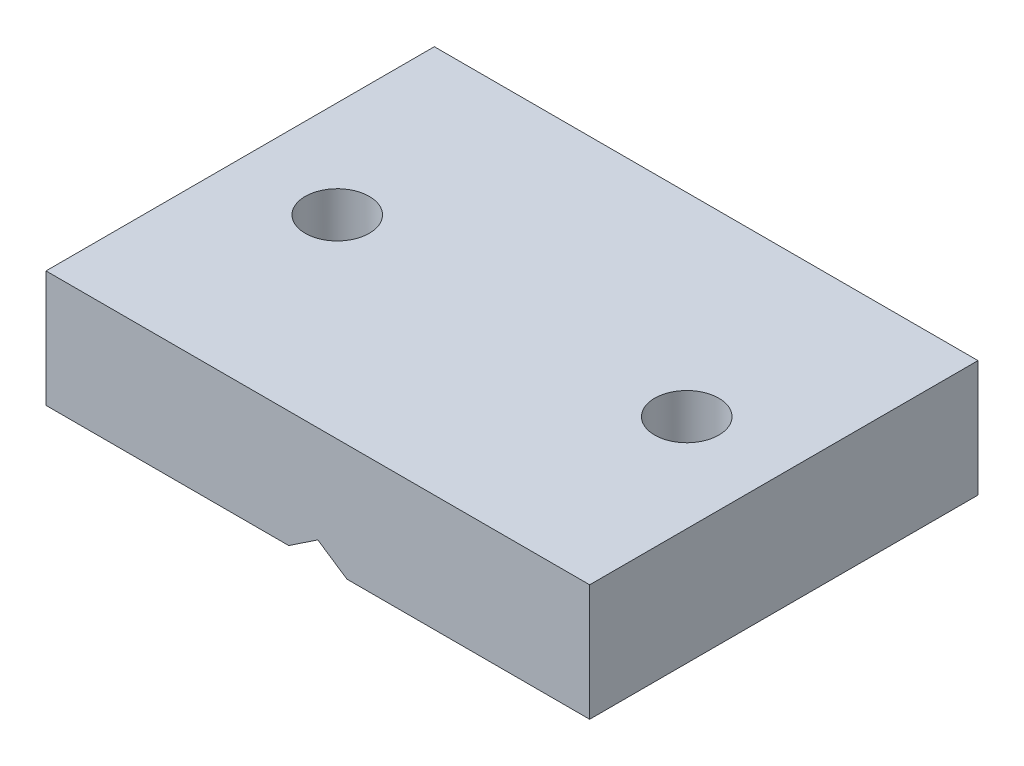
SolidWorks part; units mm, degrees
ref_plane "Plano frontal" through (0, 0, 0) normal (0, 0, 1) x (1, 0, 0)
ref_plane "Plano superior" through (0, 0, 0) normal (0, 1, 0) x (1, 0, 0)
ref_plane "Plano direito" through (0, 0, 0) normal (1, 0, 0) x (0, 0, -1)
sketch "Esboço1" plane through (0, 0, 0) normal (0, 0, 1) x (1, 0, 0)
  line L0 (-1.5, 0) -> (-14, 0)
  line L1 (-14, 0) -> (-14, 6)
  line L2 (-14, 6) -> (14, 6)
  line L3 (14, 6) -> (14, 0)
  line L4 (14, 0) -> (1.5, 0)
  line L5 (-1.5, 0) -> (0, 1)
  line L6 (0, 1) -> (1.5, 0)
  line L7 (0, 0) -> (0, 6.5547) construction
  point P11 (0, 3.1179)
  point P12 (0, 0)
  point P13 (0, 0)
  dimension "D1" = 1
  dimension "D2" = 28
  dimension "D3" = 6
  dimension "D4" = 3
extrude "Ressalto-extrusão1" add sketch "Esboço1" along normal mid plane 20
sketch "Esboço2" plane through (0, 0, 0) normal (0, -1, 0) x (1, 0, 0)
  line L0 (0, 0) -> (0, 9.5392) construction
  circle A0 centre (-9, 0) radius 1.65
  circle A1 centre (9, 0) radius 1.65
  point P5 (0, 0)
  dimension "D2" = 3.3
  dimension "D1" = 18
extrude "Corte-extrusão1" cut sketch "Esboço2" against normal blind 15
